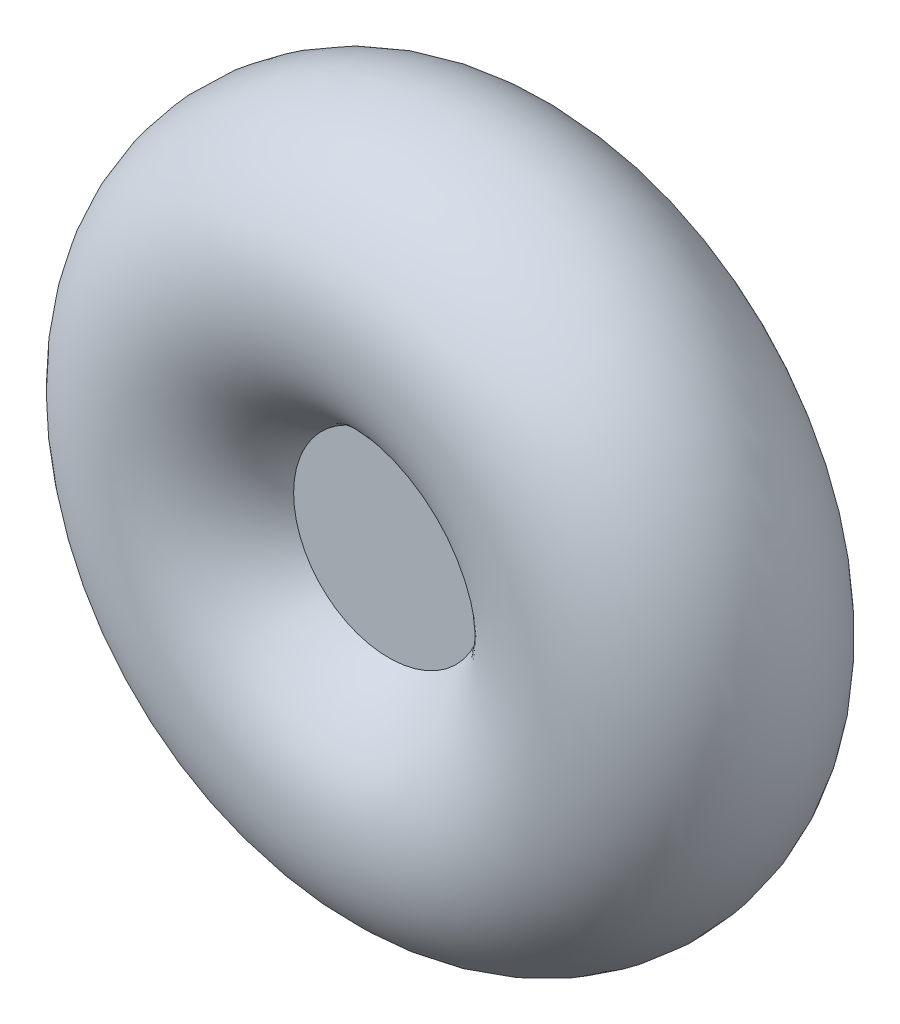
SolidWorks part; units mm, degrees
other "Markup1"
sketch "Sketch2" plane through (53.975, 53.975, -20.7655) normal (0.4987, 0.2018, -0.843) x (-0.8511, -0.0703, -0.5203)
ref_plane "Front Plane" through (0, 0, 0) normal (0, 0, 1) x (1, 0, 0)
ref_plane "Top Plane" through (0, 0, 0) normal (0, 1, 0) x (1, 0, 0)
ref_plane "Right Plane" through (0, 0, 0) normal (1, 0, 0) x (0, 0, -1)
sketch "Sketch1" plane through (0, 0, 0) normal (1, 0, 0) x (0, 0, -1)
  line L0 (0, 0) -> (0, 53.975) construction
  line L1 (0, 0) -> (-19.0058, 0) construction
  line L2 (0, 0) -> (17.8325, 0) construction
  line L4 (-9.5029, 0) -> (9.5029, 0)
  line L5 (-9.5029, 0) -> (-9.5029, 14.746)
  line L6 (-9.5029, 14.746) -> (9.5029, 14.746)
  line L7 (9.5029, 0) -> (9.5029, 14.746)
  circle A0 centre (0, 33.2095) radius 20.7655
  dimension "D3" = 41.531
  dimension "D1" = 53.975
  dimension "D2" = 19.0058
revolve "Revolve1" add sketch "Sketch1" angle 360 about L1
